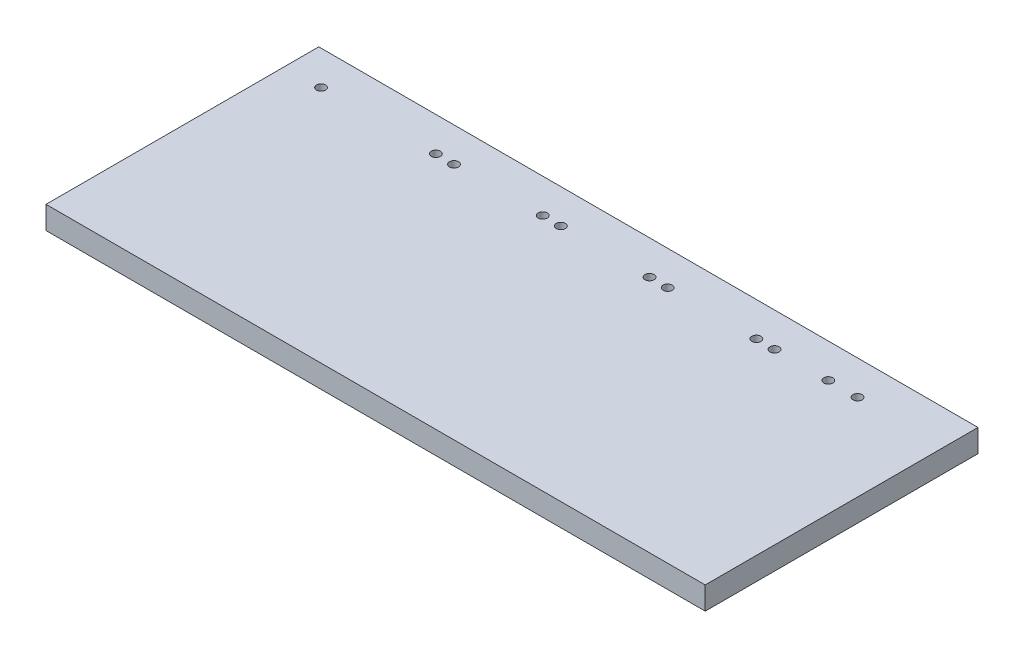
SolidWorks part; units mm, degrees
ref_plane "Спереди" through (0, 0, 0) normal (0, 0, 1) x (1, 0, 0)
ref_plane "Сверху" through (0, 0, 0) normal (0, 1, 0) x (1, 0, 0)
ref_plane "Справа" through (0, 0, 0) normal (1, 0, 0) x (0, 0, -1)
sketch "Эскиз1" plane through (0, 0, 0) normal (0, 1, 0) x (1, 0, 0)
  line L1 (0, 0) -> (290, 0)
  line L2 (0, 0) -> (0, 120)
  line L3 (0, 120) -> (290, 120)
  line L4 (290, 0) -> (290, 120)
extrude "Бобышка-Вытянуть1" add sketch "Эскиз1" along normal blind 10
sketch "Эскиз2" plane through (0, 10, 0) normal (0, 1, 0) x (1, 0, 0)
  line L0 (16, 105) -> (259.5, 105) construction
  circle A0 centre (16, 105) radius 2
  circle A1 centre (252, 105) radius 2
  circle A2 centre (66.5, 105) radius 2
  circle A3 centre (74.5, 105) radius 2
  circle A4 centre (113.5, 105) radius 2
  circle A5 centre (121.5, 105) radius 2
  circle A6 centre (160.5, 105) radius 2
  circle A7 centre (168.5, 105) radius 2
  circle A8 centre (207.5, 105) radius 2
  circle A9 centre (215.5, 105) radius 2
  circle A10 centre (239.161, 105) radius 2
extrude "Вырез-Вытянуть1" cut sketch "Эскиз2" against normal through all
